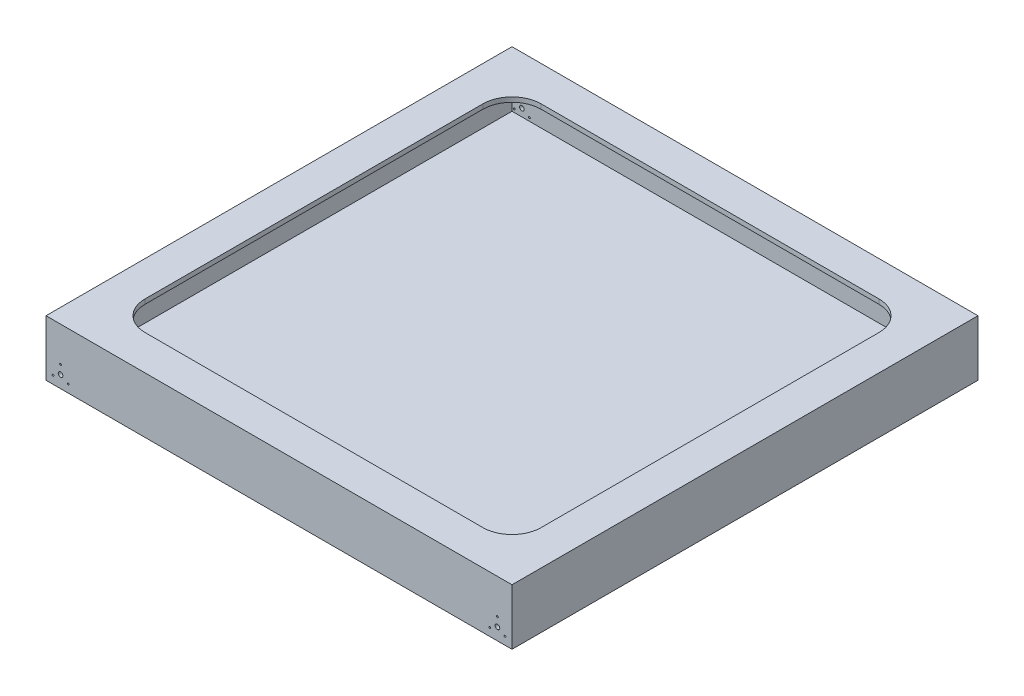
SolidWorks part; units mm, degrees
ref_plane "Front Plane" through (0, 0, 0) normal (0, 0, 1) x (1, 0, 0)
ref_plane "Top Plane" through (0, 0, 0) normal (0, 1, 0) x (1, 0, 0)
ref_plane "Right Plane" through (0, 0, 0) normal (1, 0, 0) x (0, 0, -1)
sketch "Sketch1" plane through (0, 0, 0) normal (0, 1, 0) x (1, 0, 0)
  line L1 (400, -400) -> (-400, -400)
  line L2 (400, -400) -> (400, 400)
  line L3 (400, 400) -> (-400, 400)
  line L4 (-400, -400) -> (-400, 400)
  line L5 (400, -400) -> (-400, 400) construction
  line L6 (400, 400) -> (-400, -400) construction
  point P0 (0, 0)
  dimension "D1" = 800
  dimension "D2" = 800
extrude "Boss-Extrude1" add sketch "Sketch1" along normal blind 8
sketch "Sketch2" plane through (0, 8, 0) normal (0, 1, 0) x (1, 0, 0)
  line L1 (400, -400) -> (-400, -400)
  line L2 (400, -400) -> (400, 400)
  line L3 (400, 400) -> (-400, 400)
  line L4 (-400, -400) -> (-400, 400)
  line L5 (400, -400) -> (-400, 400) construction
  line L6 (400, 400) -> (-400, -400) construction
  line L7 (392, -392) -> (-392, -392)
  line L8 (392, -392) -> (392, 392)
  line L9 (392, 392) -> (-392, 392)
  line L10 (-392, -392) -> (-392, 392)
  line L11 (392, -392) -> (-392, 392) construction
  line L12 (392, 392) -> (-392, -392) construction
  point P0 (0, 0)
  point P7 (0, 0)
  dimension "D1" = 8
extrude "Boss-Extrude2" add sketch "Sketch2" along normal blind 80
sketch "Sketch3" plane through (0, 88, 0) normal (0, 1, 0) x (1, 0, 0)
  line L1 (400, -400) -> (-400, -400)
  line L2 (400, -400) -> (400, 400)
  line L3 (400, 400) -> (-400, 400)
  line L4 (-400, -400) -> (-400, 400)
  line L5 (400, -400) -> (-400, 400) construction
  line L6 (400, 400) -> (-400, -400) construction
  line L7 (290, -340) -> (-290, -340)
  line L8 (340, -290) -> (340, 290)
  line L9 (290, 340) -> (-290, 340)
  line L10 (-340, -290) -> (-340, 290)
  line L11 (340, -340) -> (-340, 340) construction
  line L12 (340, 340) -> (-340, -340) construction
  arc A0 (340, 290) -> (290, 340) centre (290, 290) ccw
  arc A1 (290, -340) -> (340, -290) centre (290, -290) ccw
  arc A2 (-340, -290) -> (-290, -340) centre (-290, -290) ccw
  arc A3 (-290, 340) -> (-340, 290) centre (-290, 290) ccw
  point P0 (0, 0)
  point P7 (0, 0)
  dimension "D2" = 50
  dimension "D1" = 60
extrude "Boss-Extrude3" add sketch "Sketch3" along normal blind 8
sketch "Sketch4" plane through (0, 0, 400) normal (0, 0, 1) x (1, 0, 0)
  line L0 (-400, 96) -> (400, 96) construction
  line L1 (-400, 96) -> (-400, 0) construction
  line L2 (0, 0) -> (0, 300.3461) construction
  circle A0 centre (-375, 21) radius 4
  circle A1 centre (375, 21) radius 4
  dimension "D1" = 8
  dimension "D2" = 75
  dimension "D3" = 25
extrude "Cut-Extrude1" cut sketch "Sketch4" against normal blind 800
sketch "Sketch5" plane through (0, 0, 400) normal (0, 0, 1) x (1, 0, 0)
  line L0 (-375, 21) -> (-375, 85.1883) construction
  line L1 (-375, 21) -> (-371.9837, 22.7415) construction
  line L2 (-371.9837, 22.7415) -> (-375, 21) construction
  line L3 (-375, 21) -> (-375.9352, 21.5399) construction
  line L5 (0, 0) -> (0, 287.6995) construction
  line L6 (375, 21) -> (375.9352, 21.5399) construction
  line L7 (371.9837, 22.7415) -> (375, 21) construction
  line L8 (375, 21) -> (371.9837, 22.7415) construction
  line L9 (375, 21) -> (375, 85.1883) construction
  circle A0 centre (-375, 36) radius 1.5
  circle A1 centre (-387.9904, 13.5) radius 1.5
  circle A2 centre (-362.0096, 13.5) radius 1.5
  circle A3 centre (362.0096, 13.5) radius 1.5
  circle A4 centre (387.9904, 13.5) radius 1.5
  circle A5 centre (375, 36) radius 1.5
  dimension "D4" = 3
  dimension "D5" = 3
  dimension "D6" = 3
  dimension "D1" = 120
  dimension "D2" = 120
  dimension "D3" = 15
  dimension "D7" = 15
  dimension "D8" = 15
extrude "Cut-Extrude2" cut sketch "Sketch5" against normal blind 800
sketch "Sketch6" plane through (0, 0, 0) normal (0, -1, 0) x (-1, 0, 0)
  line L0 (-400, -400) -> (-400, 400) construction
  line L1 (400, -400) -> (-400, -400) construction
  line L2 (0, 0) -> (0, -642.0152) construction
  circle A0 centre (-346.85, -358.85) radius 4
  circle A1 centre (346.85, -358.85) radius 4
  dimension "D2" = 8
  dimension "D1" = 53.15
  dimension "D3" = 41.15
extrude "Cut-Extrude3" cut sketch "Sketch6" against normal blind 10
